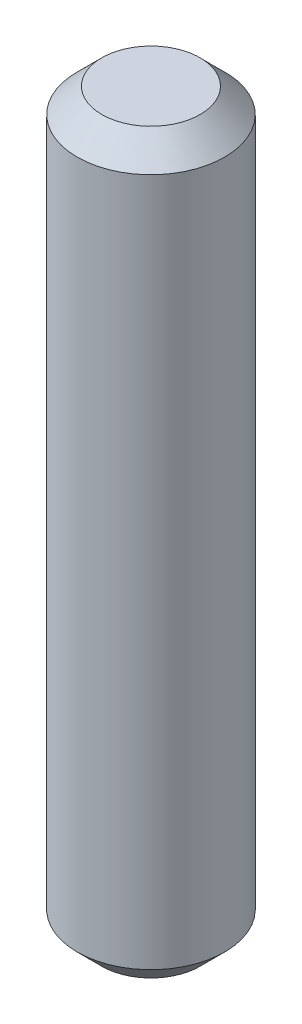
SolidWorks part; units mm, degrees
ref_plane "Front" through (0, 0, 0) normal (0, 0, 1) x (1, 0, 0)
ref_plane "Top" through (0, 0, 0) normal (0, 1, 0) x (1, 0, 0)
ref_plane "Right" through (0, 0, 0) normal (1, 0, 0) x (0, 0, -1)
sketch "Sketch1" plane through (0, 0, 0) normal (0, 1, 0) x (1, 0, 0)
  circle A0 centre (0, 0) radius 3
  dimension "D1" = 6
extrude "Boss-Extrude1" add sketch "Sketch1" along normal blind 30
chamfer "Chamfer1" distance 1 angle 45 2 edges at (0, 0, 3) (0, 30, 3)
